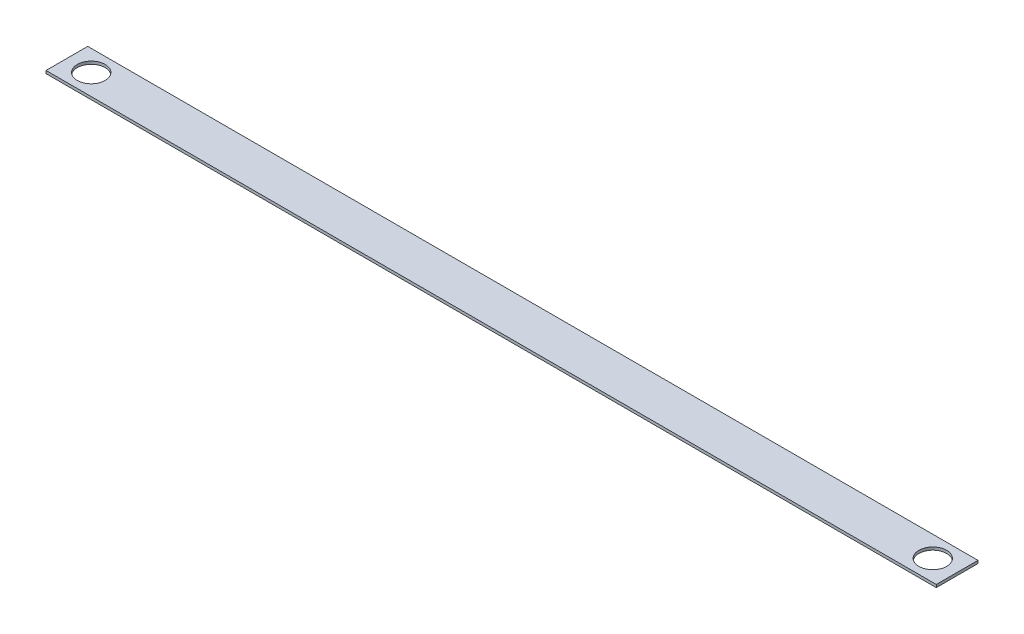
SolidWorks part; units mm, degrees
ref_plane "Front Plane" through (0, 0, 0) normal (0, 0, 1) x (1, 0, 0)
ref_plane "Top Plane" through (0, 0, 0) normal (0, 1, 0) x (1, 0, 0)
ref_plane "Right Plane" through (0, 0, 0) normal (1, 0, 0) x (0, 0, -1)
sketch "Sketch1" plane through (0, 0, 0) normal (0, 1, 0) x (1, 0, 0)
  line L1 (406.4, -19.05) -> (-406.4, -19.05)
  line L2 (406.4, -19.05) -> (406.4, 19.05)
  line L3 (406.4, 19.05) -> (-406.4, 19.05)
  line L4 (-406.4, -19.05) -> (-406.4, 19.05)
  line L5 (406.4, -19.05) -> (-406.4, 19.05) construction
  line L6 (406.4, 19.05) -> (-406.4, -19.05) construction
  point P0 (0, 0)
  dimension "D1" = 812.8
  dimension "D2" = 38.1
extrude "Boss-Extrude1" add sketch "Sketch1" along normal blind 2.54
sketch "Sketch2" plane through (0, 2.54, 0) normal (0, 1, 0) x (1, 0, 0)
  line L0 (384.175, 0) -> (-384.175, 0) construction
  circle A0 centre (-384.175, 0) radius 12.7
  circle A1 centre (384.175, 0) radius 12.7
  point P4 (0, 0)
  dimension "D2" = 25.4
  dimension "D1" = 768.35
extrude "Cut-Extrude1" cut sketch "Sketch2" against normal through all both and the other way through all
